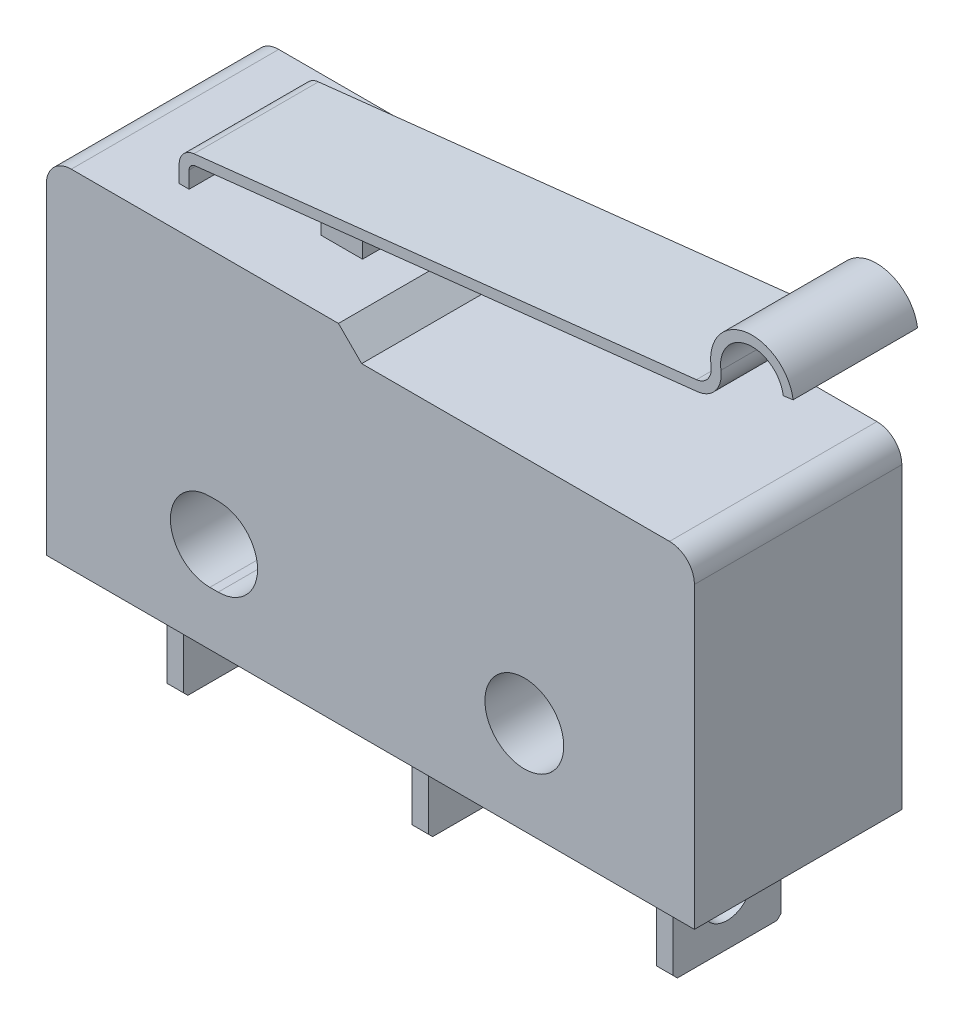
SolidWorks part; units mm, degrees
ref_plane "Front" through (0, 0, 0) normal (0, 0, 1) x (1, 0, 0)
ref_plane "Top" through (0, 0, 0) normal (0, 1, 0) x (1, 0, 0)
ref_plane "Right" through (0, 0, 0) normal (1, 0, 0) x (0, 0, -1)
sketch "Sketch2" plane through (0, 0, 0) normal (0, 0, 1) x (1, 0, 0)
  line L0 (-4.9149, 4.064) -> (-4.6609, 4.064)
  line L1 (-9.1567, 10.6172) -> (-4.9149, 10.6172)
  line L2 (-9.9187, 9.8552) -> (-9.9187, 0)
  line L3 (-9.9187, 0) -> (9.9187, 0)
  line L4 (9.9187, 9.144) -> (9.9187, 0)
  line L5 (-4.9149, 1.651) -> (-4.6609, 1.651)
  line L6 (-4.7879, 4.064) -> (-4.7879, 1.651) construction
  line L7 (4.7117, 2.8575) -> (-4.6609, 2.8575) construction
  line L8 (9.1567, 9.906) -> (-0.2667, 9.906)
  line L9 (-0.2667, 9.906) -> (-0.9779, 10.6172)
  line L10 (-0.9779, 10.6172) -> (-4.9149, 10.6172)
  line L13 (-2.9464, 10.6172) -> (-2.9464, 2.8575) construction
  line L14 (-4.9149, 10.6172) -> (-4.9149, 4.064) construction
  circle A0 centre (4.7117, 2.8575) radius 1.2065
  arc A1 (-4.9149, 4.064) -> (-4.9149, 1.651) centre (-4.9149, 2.8575) ccw
  arc A2 (-4.6609, 1.651) -> (-4.6609, 4.064) centre (-4.6609, 2.8575) ccw
  arc A3 (9.9187, 9.144) -> (9.1567, 9.906) centre (9.1567, 9.144) ccw
  arc A4 (-9.1567, 10.6172) -> (-9.9187, 9.8552) centre (-9.1567, 9.8552) ccw
  dimension "D4" = 5.207
  dimension "D5" = 2.413
  dimension "D6" = 2.667
  dimension "D7" = 9.906
  dimension "D8" = 10.6172
  dimension "D9" = 9.652
  dimension "D10" = 0.762
  dimension "D1" = 19.8374
  dimension "D2" = 2.8575
  dimension "D3" = 9.4996
  dimension "D12" = 135
extrude "Extrude1" add sketch "Sketch2" along normal mid plane 6.35
sketch "Sketch3" plane through (0, 0, 0) normal (0, 0, 1) x (1, 0, 0)
  line L0 (-3.5814, 10.6172) -> (-3.5814, 11.5246)
  line L1 (-2.9464, 10.6172) -> (-2.9464, 10.7315) construction
  line L2 (-2.3114, 11.5246) -> (-2.3114, 10.6172)
  line L3 (-2.3114, 10.6172) -> (-3.5814, 10.6172)
  line L4 (-3.5814, 11.5246) -> (-2.3114, 11.5246) construction
  line L5 (-2.9464, 10.6172) -> (-2.9464, 2.8575) construction
  line L7 (-0.9779, 10.6172) -> (-9.1567, 10.6172) construction
  arc A0 (-3.5814, 11.5246) -> (-2.3114, 11.5246) centre (-2.9464, 10.7315) cw
  arc A1 (-4.9149, 4.064) -> (-4.9149, 1.651) centre (-4.9149, 2.8575) ccw construction
  dimension "D1" = 8.89
  dimension "D3" = 1.016
  dimension "D2" = 1.27
extrude "Extrude2" add sketch "Sketch3" along normal mid plane 2.2098 separate body
ref_plane "Plane1" through (-7.493, 0, 0) normal (1, 0, 0) x (0, 0, -1)
sketch "Sketch10" plane through (-7.493, 0, 0) normal (1, 0, 0) x (0, 0, -1)
  line L0 (-1.651, 0) -> (-1.651, -3.0734)
  line L1 (-1.524, -3.2004) -> (1.524, -3.2004)
  line L2 (1.651, -3.0734) -> (1.651, 0)
  line L3 (1.651, 0) -> (-1.651, 0)
  line L4 (0, -3.2004) -> (0, -1.6764) construction
  line L5 (0, 0) -> (0, -1.6764) construction
  line L6 (-1.651, -3.0734) -> (-1.524, -3.2004)
  line L7 (1.524, -3.2004) -> (1.651, -3.0734)
  circle A0 centre (0, -1.6764) radius 0.762
  point P1 (-1.651, -3.2004)
  point P3 (1.651, -3.2004)
  dimension "D2" = 1.524
  dimension "D1" = 3.2004
  dimension "D3" = 3.302
  dimension "D4" = 1.524
  dimension "D5" = 0.127
  dimension "D6" = 45
  dimension "D7" = 0.127
  dimension "D8" = 45
extrude "Extrude6" add sketch "Sketch10" along normal mid plane 0.508
pattern_linear "LPattern1" count 3 spacing 7.493 along (1, 0, 0) of "Extrude6"
sketch "Sketch11" plane through (0, 0, 0) normal (0, 0, 1) x (1, 0, 0)
  line L0 (-7.1247, 10.6172) -> (-7.1247, 11.1283)
  line L1 (-0.9779, 10.6172) -> (-9.1567, 10.6172) construction
  line L2 (-6.6726, 11.6332) -> (8.7112, 13.335)
  line L3 (-9.9187, 9.8552) -> (-9.9187, 0) construction
  line L4 (-9.9187, 0) -> (9.9187, 0) construction
  line L5 (9.158, 13.9134) -> (11.6713, 14.2806) construction
  arc A0 (-7.1247, 11.1283) -> (-6.6726, 11.6332) centre (-6.6167, 11.1283) cw
  arc A1 (9.158, 13.9134) -> (11.6713, 14.2806) centre (10.4146, 14.097) cw
  arc A2 (8.7112, 13.335) -> (9.158, 13.9134) centre (8.6553, 13.8399) ccw
  dimension "D4" = 1.27
  dimension "D5" = 0.508
  dimension "D1" = 2.794
  dimension "D2" = 15.367
  dimension "D3" = 21.59
  dimension "D6" = 1.016
  dimension "D7" = 13.335
extrude "Extrude-Thin1" add sketch "Sketch11" along normal mid plane 3.81 thin
